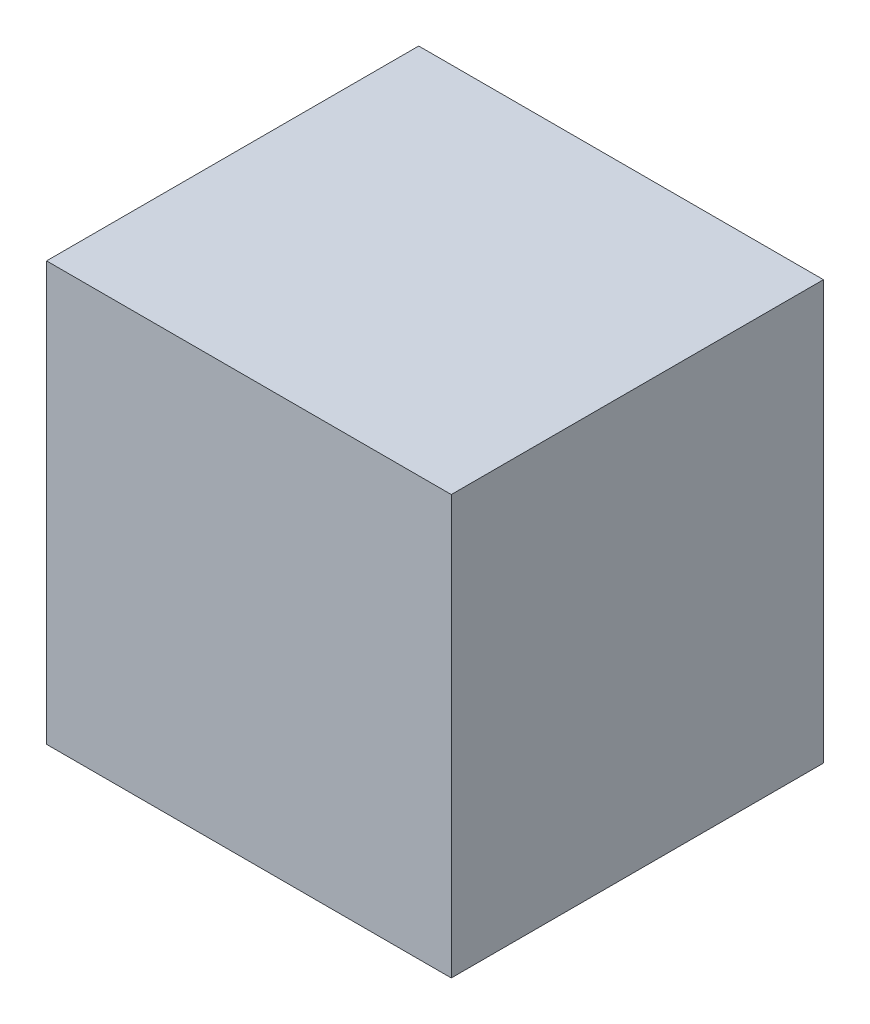
SolidWorks part; units mm, degrees
ref_plane "前视基准面" through (0, 0, 0) normal (0, 0, 1) x (1, 0, 0)
ref_plane "上视基准面" through (0, 0, 0) normal (0, 1, 0) x (1, 0, 0)
ref_plane "右视基准面" through (0, 0, 0) normal (1, 0, 0) x (0, 0, -1)
sketch "草图1" plane through (0, 0, 0) normal (0, 0, 1) x (1, 0, 0)
  line L0 (-34.57, -9.5751) -> (400.43, -9.5751)
  line L1 (400.43, -9.5751) -> (400.43, 440.4249)
  line L2 (400.43, 440.4249) -> (-34.57, 440.4249)
  line L3 (-34.57, 440.4249) -> (-34.57, -9.5751)
  dimension "D1" = 435
  dimension "D2" = 450
extrude "凸台-拉伸1" add sketch "草图1" along normal blind 400
